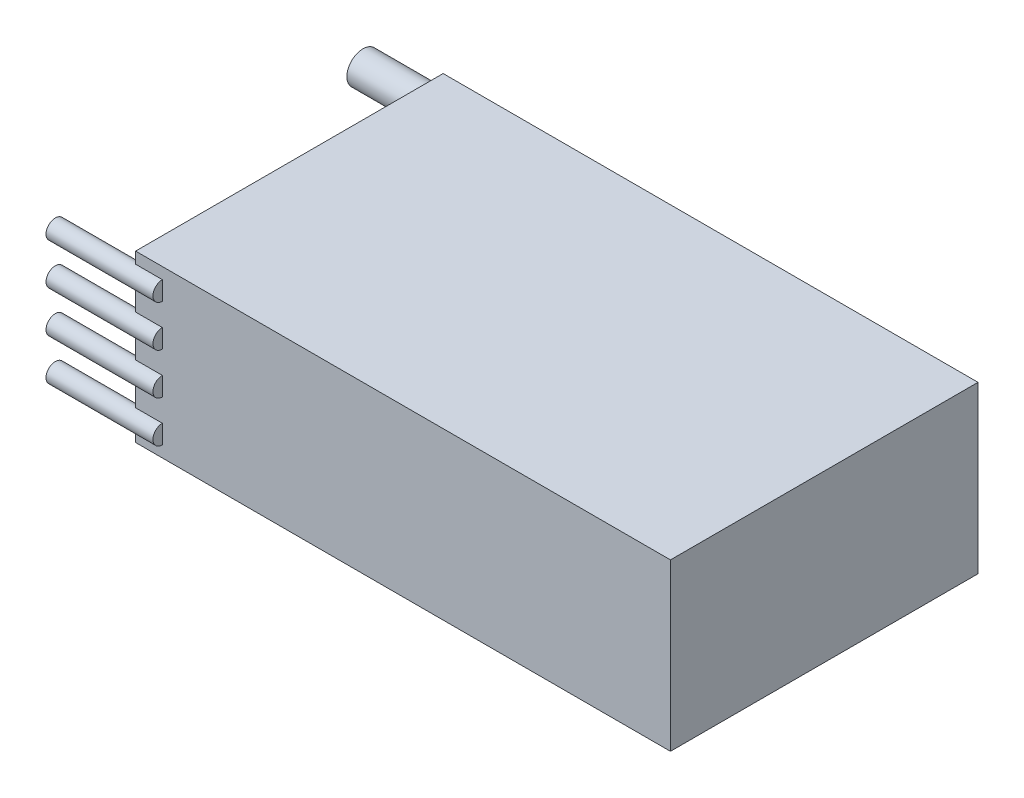
SolidWorks part; units mm, degrees
ref_plane "Front Plane" through (0, 0, 0) normal (0, 0, 1) x (1, 0, 0)
ref_plane "Top Plane" through (0, 0, 0) normal (0, 1, 0) x (1, 0, 0)
ref_plane "Right Plane" through (0, 0, 0) normal (1, 0, 0) x (0, 0, -1)
sketch "Sketch1" plane through (0, 0, 0) normal (0, 1, 0) x (1, 0, 0)
  line L1 (25.4, -14.605) -> (-25.4, -14.605)
  line L2 (25.4, -14.605) -> (25.4, 14.605)
  line L3 (25.4, 14.605) -> (-25.4, 14.605)
  line L4 (-25.4, -14.605) -> (-25.4, 14.605)
  line L5 (25.4, -14.605) -> (-25.4, 14.605) construction
  line L6 (25.4, 14.605) -> (-25.4, -14.605) construction
  point P0 (0, 0)
  dimension "D1" = 29.21
  dimension "D2" = 50.8
extrude "Boss-Extrude1" add sketch "Sketch1" along normal blind 15.748
sketch "Sketch2" plane through (-25.4, 0, 0) normal (-1, 0, 0) x (0, 0, 1)
  line L0 (-14.605, 15.748) -> (-14.605, 0) construction
  line L1 (-14.605, 7.874) -> (14.605, 7.874) construction
  line L2 (14.605, 15.748) -> (14.605, 0) construction
  line L3 (0, 0) -> (0, 15.748) construction
  line L4 (-14.605, 15.748) -> (14.605, 15.748) construction
  line L5 (14.605, 11.811) -> (14.605, 7.874) construction
  line L6 (14.605, 11.811) -> (0, 11.811) construction
  circle A1 centre (-14.605, 12.446) radius 1.524
  circle A2 centre (14.605, 9.8425) radius 0.889
  circle A3 centre (14.605, 13.7795) radius 0.889
  circle A4 centre (14.605, 5.9055) radius 0.889
  circle A5 centre (14.605, 1.9685) radius 0.889
  circle A6 centre (-14.605, 3.302) radius 1.524
  dimension "D1" = 3.048
  dimension "D3" = 1.778
  dimension "D2" = 4.572
extrude "Boss-Extrude2" add sketch "Sketch2" along normal blind 7.62 and the other way blind 2.54
